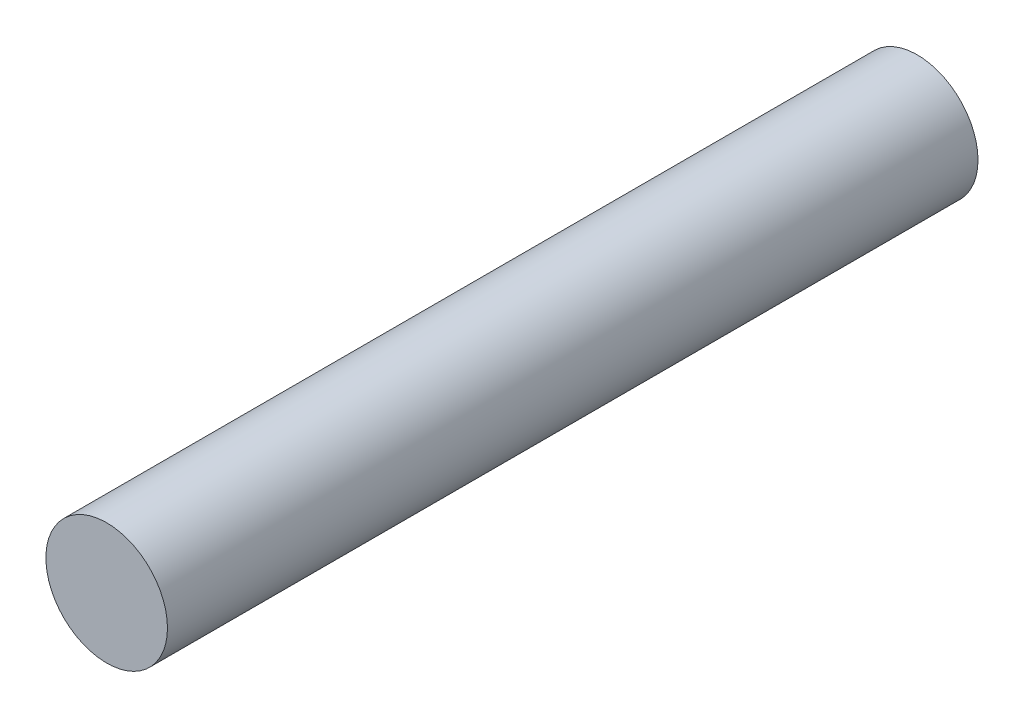
SolidWorks part; units mm, degrees
ref_plane "Plan de face" through (0, 0, 0) normal (0, 0, 1) x (1, 0, 0)
ref_plane "Plan de dessus" through (0, 0, 0) normal (0, 1, 0) x (1, 0, 0)
ref_plane "Plan de droite" through (0, 0, 0) normal (1, 0, 0) x (0, 0, -1)
sketch "Esquisse1" plane through (0, 0, 0) normal (0, 0, 1) x (1, 0, 0)
  circle A0 centre (0, 0) radius 1.5
  dimension "D1" = 3
extrude "Boss.-Extru.1" add sketch "Esquisse1" along normal blind 20
